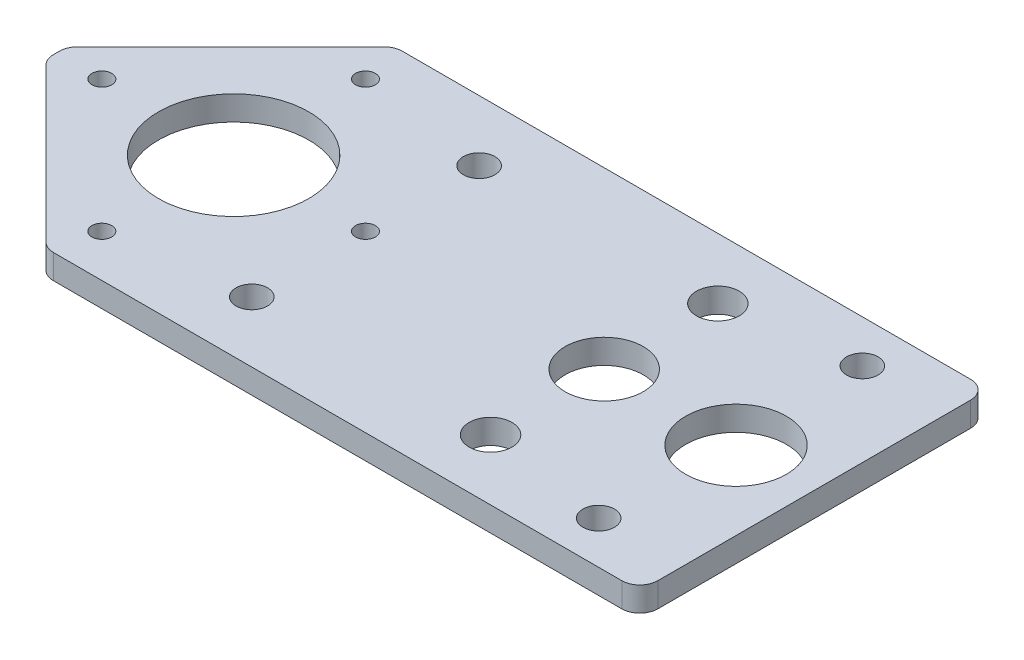
SolidWorks part; units mm, degrees
material "6061-T6 (SS)"
ref_plane "Front Plane" through (0, 0, 0) normal (0, 0, 1) x (1, 0, 0)
ref_plane "Top Plane" through (0, 0, 0) normal (0, 1, 0) x (1, 0, 0)
ref_plane "Right Plane" through (0, 0, 0) normal (1, 0, 0) x (0, 0, -1)
ref_plane "Plane1" through (0, 0, 0) normal (0, -1, 0) x (1, 0, 0)
sketch "Sketch1" plane through (0, 0, 0) normal (0, -1, 0) x (1, 0, 0)
  line L0 (0, -26) -> (0, 26)
  line L1 (-3, 29) -> (-97.5, 29)
  line L2 (-99.6213, 28.1213) -> (-125.1213, 2.6213)
  line L3 (-126, 0.5) -> (-126, -0.5)
  line L4 (-125.1213, -2.6213) -> (-99.6213, -28.1213)
  line L5 (-97.5, -29) -> (-3, -29)
  line L6 (-118.4607, 0) -> (-96.5404, -21.9203) construction
  line L7 (-118.4607, 0) -> (-96.5404, 21.9203) construction
  line L8 (-96.5404, 21.9203) -> (-74.6201, 0) construction
  line L9 (-74.6201, 0) -> (-96.5404, -21.9203) construction
  line L10 (-118.4607, 0) -> (-74.6201, 0) construction
  line L11 (-74.6201, 18.9) -> (-74.6201, -18.9) construction
  line L12 (-13.9201, 21.9203) -> (-13.9201, -21.9203) construction
  line L13 (-34.9201, 18.9) -> (-34.9201, -18.9) construction
  line L14 (-96.5404, 21.9203) -> (-96.5404, -21.9203) construction
  line L15 (0, 0) -> (-170.4406, 0) construction
  circle A0 centre (-13, 0) radius 8.375
  circle A1 centre (-34.9201, 18.9) radius 3.56
  circle A2 centre (-74.6201, 18.9) radius 2.625
  circle A3 centre (-34.9201, -18.9) radius 3.56
  circle A4 centre (-74.6201, -18.9) radius 2.625
  circle A5 centre (-96.5404, 0) radius 12.5
  circle A6 centre (-74.6201, 0) radius 1.65
  circle A7 centre (-118.4607, 0) radius 1.65
  circle A8 centre (-96.5404, -21.9203) radius 1.65
  circle A9 centre (-96.5404, 21.9203) radius 1.65
  circle A10 centre (-13.9201, 21.9203) radius 2.625
  circle A11 centre (-13.9201, -21.9203) radius 2.625
  circle A12 centre (-34.9201, 0) radius 6.5
  arc A13 (-3, -29) -> (0, -26) centre (-3, -26) ccw
  arc A14 (0, 26) -> (-3, 29) centre (-3, 26) ccw
  arc A15 (-97.5, 29) -> (-99.6213, 28.1213) centre (-97.5, 26) ccw
  arc A16 (-125.1213, 2.6213) -> (-126, 0.5) centre (-123, 0.5) ccw
  arc A17 (-126, -0.5) -> (-125.1213, -2.6213) centre (-123, -0.5) ccw
  arc A18 (-99.6213, -28.1213) -> (-97.5, -29) centre (-97.5, -26) ccw
  point P46 (-96.5404, 0)
  dimension "D3" = 3
  dimension "D4" = 3
  dimension "D9" = 16.75
  dimension "D10" = 3.3
  dimension "D11" = 7.12
  dimension "D12" = 5.25
  dimension "D13" = 25
  dimension "D14" = 13
  dimension "D1" = 58
  dimension "D2" = 126
  dimension "D5" = 45
  dimension "D6" = 13
  dimension "D7" = 21
  dimension "D8" = 39.7
  dimension "D15" = 31
  dimension "D16" = 31
  dimension "D17" = 1.8402
  dimension "D18" = 10.1
  dimension "D19" = 43.8406
  dimension "D20" = 37.8
  dimension "D22" = 45
  dimension "D23" = 94.5
  dimension "D24" = 21.9203
  dimension "D25" = 7.5393
  dimension "D26" = 6.5633
extrude "Boss-Extrude1" add sketch "Sketch1" against normal blind 4.064
